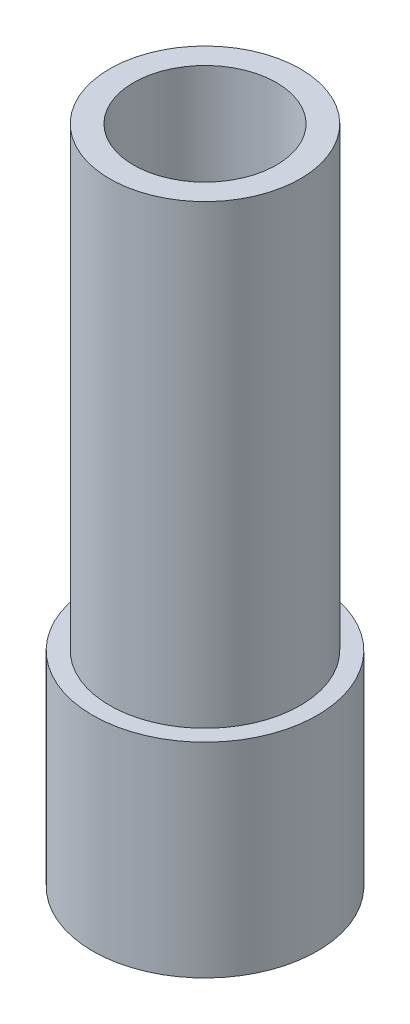
SolidWorks part; units mm, degrees
ref_plane "Front Plane" through (0, 0, 0) normal (0, 0, 1) x (1, 0, 0)
ref_plane "Top Plane" through (0, 0, 0) normal (0, 1, 0) x (1, 0, 0)
ref_plane "Right Plane" through (0, 0, 0) normal (1, 0, 0) x (0, 0, -1)
sketch "Sketch2" plane through (0, 0, 0) normal (0, 0, 1) x (1, 0, 0)
  line L0 (10.5, 0) -> (4.5, 0)
  line L1 (10.5, 0) -> (10.5, 86)
  line L2 (4.5, 0) -> (4.5, -6)
  line L3 (4.5, -6) -> (13.5, -6)
  line L4 (16.5, -6) -> (16.5, -11)
  line L5 (16.5, -11) -> (13.5, -11)
  line L6 (13.5, -11) -> (13.5, -6)
  line L7 (16.5, -6) -> (16.5, 19)
  line L8 (0, 0) -> (0, 104.8538) construction
  line L9 (14, 86) -> (14, 19)
  line L10 (16.5, 19) -> (14, 19)
  line L11 (10.5, 86) -> (14, 86)
revolve "Revolve1" add sketch "Sketch2" angle 360 about L8
